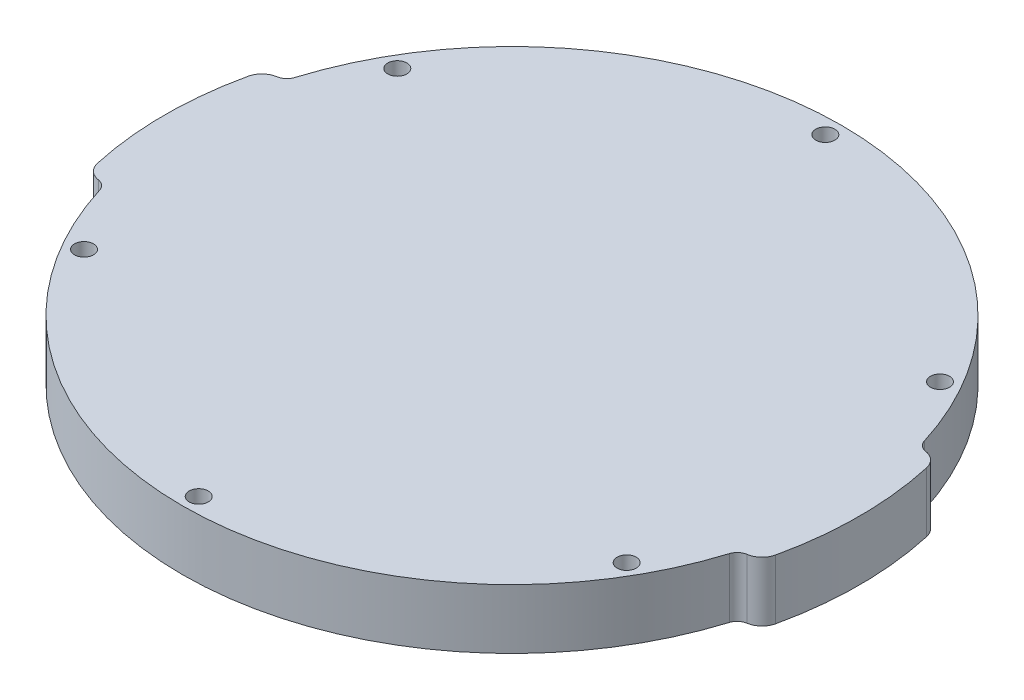
SolidWorks part; units mm, degrees
ref_plane "前视" through (0, 0, 0) normal (0, 0, 1) x (1, 0, 0)
ref_plane "上视" through (0, 0, 0) normal (0, 1, 0) x (1, 0, 0)
ref_plane "右视" through (0, 0, 0) normal (1, 0, 0) x (0, 0, -1)
sketch "草图1" plane through (0, 0, 0) normal (0, 1, 0) x (1, 0, 0)
  line L0 (0, 0) -> (-58.25, 0) construction
  line L1 (0, 0) -> (58.25, 0) construction
  line L2 (-62.1675, 15) -> (67.4067, 15) construction
  line L3 (-75.5235, -15) -> (71.1812, -15) construction
  line L4 (0, 0) -> (0, 55.25) construction
  line L5 (0, 0) -> (0, -55.25) construction
  line L6 (-53.1748, -15) -> (-56.2855, -15)
  line L7 (53.1748, 15) -> (56.2855, 15)
  line L8 (-58.25, -15.6796) -> (-58.25, 17.35) construction
  line L9 (58.25, -19.0201) -> (58.25, 20.677) construction
  line L10 (56.2855, -15) -> (53.1748, -15)
  arc A0 (0, 55.25) -> (-53.1748, 15) centre (0, 0) ccw
  arc A1 (0, 55.25) -> (53.1748, 15) centre (0, 0) cw
  arc A2 (0, -55.25) -> (53.1748, -15) centre (0, 0) ccw
  arc A3 (0, -55.25) -> (-53.1748, -15) centre (0, 0) cw
  arc A4 (-58.25, 0) -> (-56.2855, 15) centre (0, 0) cw
  arc A5 (-58.25, 0) -> (-56.2855, -15) centre (0, 0) ccw
  arc A6 (58.25, 0) -> (56.2855, 15) centre (0, 0) ccw
  arc A7 (58.25, 0) -> (56.2855, -15) centre (0, 0) cw
  spline S0 degree 1 poles (-56.2855, 15) (-53.1748, 15) knots 0 0 1 1
  dimension "D1" = 15
  dimension "D2" = 15
  dimension "D3" = 55.25
  dimension "D4" = 55.25
extrude "凸台-拉伸1" add sketch "草图1" along normal blind 10 contours A0 S0 A4 A5 L6 A3 A2 L10 A7 A6 L7 A1
fillet "圆角2" radius 3 4 edges at (-56.2855, 5, -15) (56.2855, 5, -15) (56.2855, 5, 15) (-56.2855, 5, 15)
fillet "圆角3" radius 2 4 edges at (-53.1748, 5, -15) (53.1748, 5, -15) (53.1748, 5, 15) (-53.1748, 5, 15)
sketch "草图2" plane through (0, 0, 0) normal (0, -1, 0) x (1, 0, 0)
  line L0 (0, 65.3225) -> (0, -64.5242) construction
  circle A0 centre (0, 0) radius 52.525
  circle A1 centre (0, 52.525) radius 1.6
  circle A2 centre (45.488, 26.2625) radius 1.6
  circle A3 centre (45.488, -26.2625) radius 1.6
  circle A4 centre (0, -52.525) radius 1.6
  circle A5 centre (-45.488, -26.2625) radius 1.6
  circle A6 centre (-45.488, 26.2625) radius 1.6
  point P20 (0, 0)
  dimension "D1" = 105.05
  dimension "D2" = 6
  dimension "D3" = 3.2
extrude "切除-拉伸1" cut sketch "草图2" against normal through all contours A1 | A6 | A5 | A4 | A3 | A2
